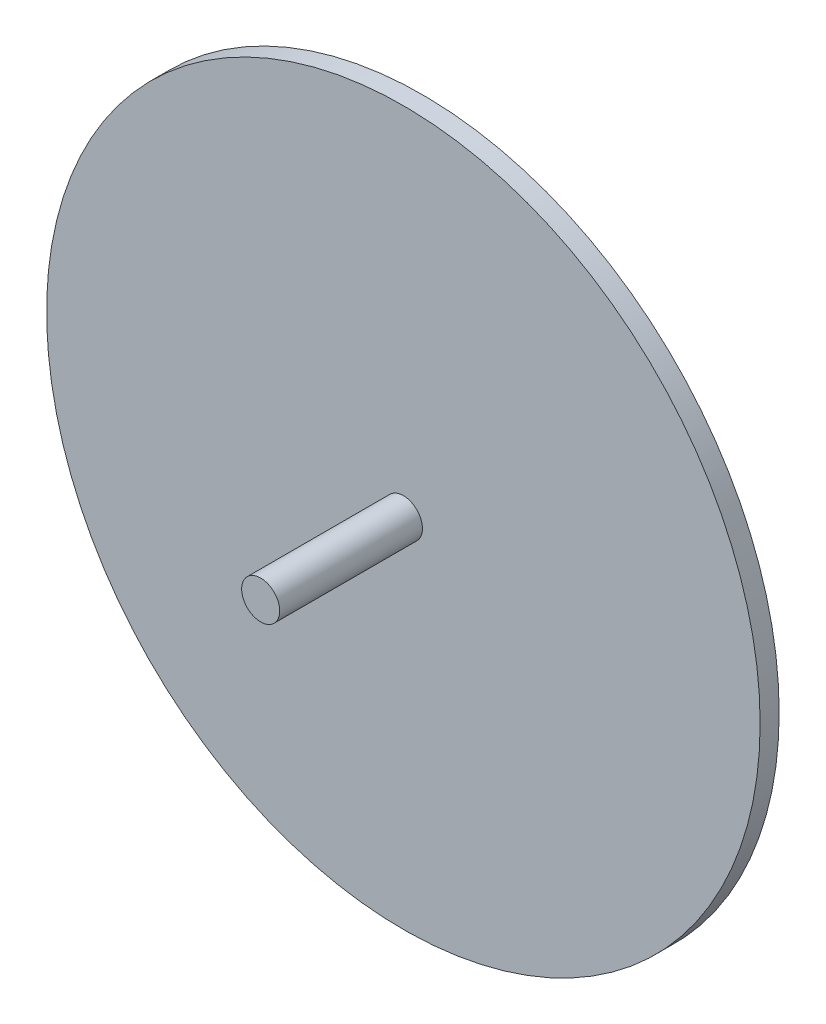
SolidWorks part; units mm, degrees
ref_plane "Front Plane" through (0, 0, 0) normal (0, 0, 1) x (1, 0, 0)
ref_plane "Top Plane" through (0, 0, 0) normal (0, 1, 0) x (1, 0, 0)
ref_plane "Right Plane" through (0, 0, 0) normal (1, 0, 0) x (0, 0, -1)
sketch "Sketch2" plane through (0, 0, 0) normal (0, 0, 1) x (1, 0, 0)
  circle A0 centre (0, 0) radius 75
  dimension "D1" = 150
extrude "Boss-Extrude1" add sketch "Sketch2" along normal blind 4
sketch "Sketch3" plane through (0, 0, 4) normal (0, 0, 1) x (1, 0, 0)
  circle A0 centre (0, 0) radius 4
  dimension "D1" = 8
extrude "Boss-Extrude2" add sketch "Sketch3" along normal blind 30
